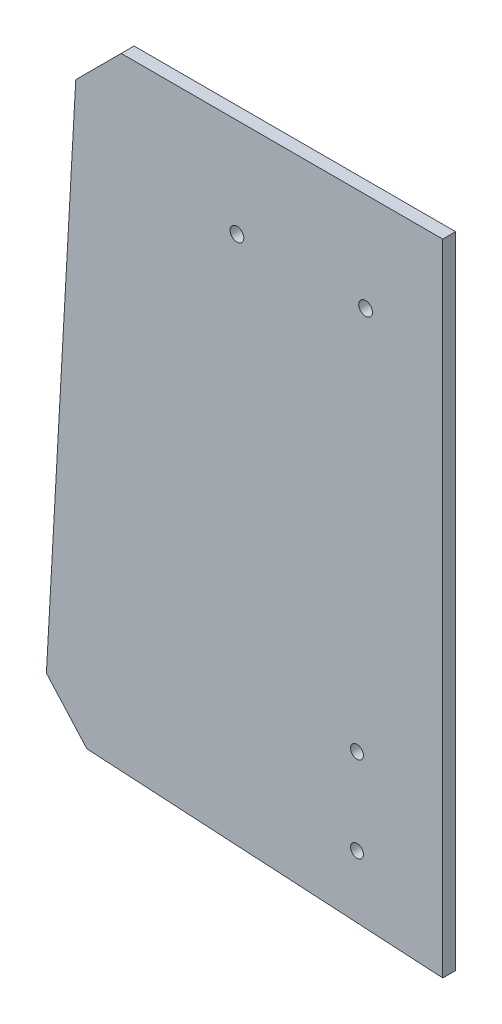
SolidWorks part; units mm, degrees
material "Acrylic (Medium-high impact)"
ref_plane "前视基准面" through (0, 0, 0) normal (0, 0, 1) x (1, 0, 0)
ref_plane "上视基准面" through (0, 0, 0) normal (0, 1, 0) x (1, 0, 0)
ref_plane "右视基准面" through (0, 0, 0) normal (1, 0, 0) x (0, 0, -1)
sketch "Sketch1" plane through (0, 0, 0) normal (0, 0, 1) x (1, 0, 0)
  line L0 (3, 33.3553) -> (3, -115.8961)
  line L1 (3, 35.3553) -> (3, -120.2082) construction
  line L2 (3, -115.8961) -> (-90, -110.5317)
  line L3 (-90, -110.5317) -> (-82, 33.3553)
  line L4 (-82, 33.3553) -> (3, 33.3553)
  line L5 (0, 35.3553) -> (3, 35.3553) construction
  line L6 (3, -75.2082) -> (3, -105.2082)
  circle A0 centre (-17, -100.2082) radius 1.5 construction
  circle A1 centre (-17, -80.2082) radius 1.5 construction
  circle A2 centre (-15, 10.3553) radius 1.6 construction
  circle A3 centre (-45, 10.3553) radius 1.6 construction
  circle A4 centre (-17, -100.2082) radius 1.5
  circle A5 centre (-17, -80.2082) radius 1.5
  circle A6 centre (-15, 10.3553) radius 1.6
  circle A7 centre (-45, 10.3553) radius 1.6
  dimension "D1" = 2
  dimension "D2" = 85
  dimension "D3" = 93
  dimension "D4" = 90.119
  dimension "D5" = 86.699
extrude "Boss-Extrude1" add sketch "Sketch1" along normal blind 3 contours L4 L3 L2 L0 A7 A6 A5 A4
chamfer "Chamfer1" distance 10 angle 45 2 edges at (-82, 33.3553, 1.5) (-90, -110.5317, 1.5)
